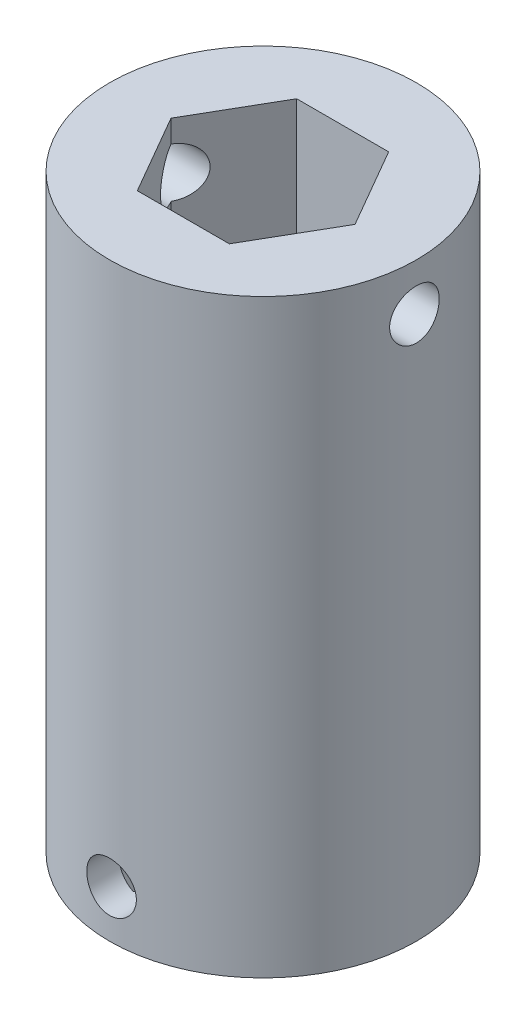
SolidWorks part; units mm, degrees
ref_plane "Front Plane" through (0, 0, 0) normal (0, 0, 1) x (1, 0, 0)
ref_plane "Top Plane" through (0, 0, 0) normal (0, 1, 0) x (1, 0, 0)
ref_plane "Right Plane" through (0, 0, 0) normal (1, 0, 0) x (0, 0, -1)
sketch "Sketch1" plane through (0, 0, 0) normal (0, 1, 0) x (1, 0, 0)
  line L1 (7.7942, 0) -> (3.8971, 6.75)
  line L2 (3.8971, 6.75) -> (-3.8971, 6.75)
  line L3 (-3.8971, 6.75) -> (-7.7942, 0)
  line L4 (-7.7942, 0) -> (-3.8971, -6.75)
  line L5 (-3.8971, -6.75) -> (3.8971, -6.75)
  line L6 (3.8971, -6.75) -> (7.7942, 0)
  circle A0 centre (0, 0) radius 13
  circle A1 centre (0, 0) radius 6.75 construction
  dimension "D2" = 26
  dimension "D1" = 13.5
extrude "Boss-Extrude1" add sketch "Sketch1" along normal blind 30
sketch "Sketch2" plane through (0, 0, 0) normal (0, -1, 0) x (1, 0, 0)
  circle A0 centre (0, 0) radius 13
  dimension "D1" = 26
extrude "Boss-Extrude2" add sketch "Sketch2" along normal blind 20
sketch "Sketch3" plane through (0, -20, 0) normal (0, -1, 0) x (1, 0, 0)
  arc A0 (-6.2438, 8.2671) -> (-5.2142, 5.3944) centre (2.4553, 9.7641) ccw
  arc A1 (-5.2142, 5.3944) -> (-5.5757, 5.0199) centre (0, 0) ccw
  arc A2 (-5.5757, 5.0199) -> (-8.483, 5.9471) centre (-9.671, -2.7995) ccw
  arc A3 (-8.483, 5.9471) -> (-9.2124, 4.7393) centre (0, 0) ccw
  arc A4 (-9.2124, 4.7393) -> (-7.0384, 2.5978) centre (-2.0244, 9.8624) ccw
  arc A5 (-7.0384, 2.5978) -> (-7.2016, 2.1036) centre (0, 0) ccw
  arc A6 (-7.2016, 2.1036) -> (-10.2233, 1.6775) centre (-7.4986, -6.7184) ccw
  arc A7 (-10.2233, 1.6775) -> (-10.3564, 0.2728) centre (0, 0) ccw
  arc A8 (-10.3564, 0.2728) -> (-7.4685, -0.7133) centre (-6.103, 8.0074) ccw
  arc A9 (-7.4685, -0.7133) -> (-7.4011, -1.2294) centre (0, 0) ccw
  arc A10 (-7.4011, -1.2294) -> (-9.9387, -2.9243) centre (-3.841, -9.3066) ccw
  arc A11 (-9.9387, -2.9243) -> (-9.4492, -4.2477) centre (0, 0) ccw
  arc A12 (-9.4492, -4.2477) -> (-6.4194, -3.8831) centre (-8.9729, 4.5664) ccw
  arc A13 (-6.4194, -3.8831) -> (-6.1347, -4.3188) centre (0, 0) ccw
  arc A14 (-6.1347, -4.3188) -> (-7.6857, -6.947) centre (0.5773, -10.0515) ccw
  arc A15 (-7.6857, -6.947) -> (-6.6704, -7.9269) centre (0, 0) ccw
  arc A16 (-6.6704, -7.9269) -> (-4.0989, -6.2838) centre (-10.0656, 0.221) ccw
  arc A17 (-4.0989, -6.2838) -> (-3.6533, -6.5529) centre (0, 0) ccw
  arc A18 (-3.6533, -6.5529) -> (-3.9104, -9.5937) centre (4.8813, -8.8056) ccw
  arc A19 (-3.9104, -9.5937) -> (-2.5705, -10.036) centre (0, 0) ccw
  arc A20 (-2.5705, -10.036) -> (-0.9665, -7.44) centre (-9.1647, -4.1682) ccw
  arc A21 (-0.9665, -7.44) -> (-0.4483, -7.4891) centre (0, 0) ccw
  arc A22 (-0.4483, -7.4891) -> (0.6394, -10.3402) centre (8.2185, -5.8156) ccw
  arc A23 (0.6394, -10.3402) -> (2.0385, -10.1575) centre (0, 0) ccw
  arc A24 (2.0385, -10.1575) -> (2.3573, -7.1225) centre (-6.4486, -7.7318) ccw
  arc A25 (2.3573, -7.1225) -> (2.8455, -6.942) centre (0, 0) ccw
  arc A26 (2.8455, -6.942) -> (5.0626, -9.0388) centre (9.9279, -1.6738) ccw
  arc A27 (5.0626, -9.0388) -> (6.2438, -8.2671) centre (0, 0) ccw
  arc A28 (6.2438, -8.2671) -> (5.2142, -5.3944) centre (-2.4553, -9.7641) ccw
  arc A29 (5.2142, -5.3944) -> (5.5757, -5.0199) centre (0, 0) ccw
  arc A30 (5.5757, -5.0199) -> (8.483, -5.9471) centre (9.671, 2.7995) ccw
  arc A31 (8.483, -5.9471) -> (9.2124, -4.7393) centre (0, 0) ccw
  arc A32 (9.2124, -4.7393) -> (7.0384, -2.5978) centre (2.0244, -9.8624) ccw
  arc A33 (7.0384, -2.5978) -> (7.2016, -2.1036) centre (0, 0) ccw
  arc A34 (7.2016, -2.1036) -> (10.2233, -1.6775) centre (7.4986, 6.7184) ccw
  arc A35 (10.2233, -1.6775) -> (10.3564, -0.2728) centre (0, 0) ccw
  arc A36 (10.3564, -0.2728) -> (7.4685, 0.7133) centre (6.103, -8.0074) ccw
  arc A37 (7.4685, 0.7133) -> (7.4011, 1.2294) centre (0, 0) ccw
  arc A38 (7.4011, 1.2294) -> (9.9387, 2.9243) centre (3.841, 9.3066) ccw
  arc A39 (9.9387, 2.9243) -> (9.4492, 4.2477) centre (0, 0) ccw
  arc A40 (9.4492, 4.2477) -> (6.4194, 3.8831) centre (8.9729, -4.5664) ccw
  arc A41 (6.4194, 3.8831) -> (6.1347, 4.3188) centre (0, 0) ccw
  arc A42 (6.1347, 4.3188) -> (7.6857, 6.947) centre (-0.5773, 10.0515) ccw
  arc A43 (7.6857, 6.947) -> (6.6704, 7.9269) centre (0, 0) ccw
  arc A44 (6.6704, 7.9269) -> (4.0989, 6.2838) centre (10.0656, -0.221) ccw
  arc A45 (4.0989, 6.2838) -> (3.6533, 6.5529) centre (0, 0) ccw
  arc A46 (3.6533, 6.5529) -> (3.9104, 9.5937) centre (-4.8813, 8.8056) ccw
  arc A47 (3.9104, 9.5937) -> (2.5705, 10.036) centre (0, 0) ccw
  arc A48 (2.5705, 10.036) -> (0.9665, 7.44) centre (9.1647, 4.1682) ccw
  arc A49 (0.9665, 7.44) -> (0.4483, 7.4891) centre (0, 0) ccw
  arc A50 (0.4483, 7.4891) -> (-0.6394, 10.3402) centre (-8.2185, 5.8156) ccw
  arc A51 (-0.6394, 10.3402) -> (-2.0385, 10.1575) centre (0, 0) ccw
  arc A52 (-2.0385, 10.1575) -> (-2.3573, 7.1225) centre (6.4486, 7.7318) ccw
  arc A53 (-2.3573, 7.1225) -> (-2.8455, 6.942) centre (0, 0) ccw
  arc A54 (-2.8455, 6.942) -> (-5.0626, 9.0388) centre (-9.9279, 1.6738) ccw
  arc A55 (-5.0626, 9.0388) -> (-6.2438, 8.2671) centre (0, 0) ccw
  arc A57 (-5.5304, 4.7688) -> (-8.3889, 5.7316) centre (-9.671, -2.7995) ccw
  arc A58 (-4.9617, 5.358) -> (-5.5304, 4.7688) centre (0, 0) ccw
  arc A59 (-6.0251, 8.1807) -> (-4.9617, 5.358) centre (2.4553, 9.7641) ccw
  arc A60 (-5.0713, 8.8038) -> (-6.0251, 8.1807) centre (0, 0) ccw
  arc A61 (-2.9136, 6.6961) -> (-5.0713, 8.8038) centre (-9.9279, 1.6738) ccw
  arc A62 (-2.1455, 6.9802) -> (-2.9136, 6.6961) centre (0, 0) ccw
  arc A63 (-1.879, 9.9847) -> (-2.1455, 6.9802) centre (6.4486, 7.7318) ccw
  arc A64 (-0.7492, 10.1323) -> (-1.879, 9.9847) centre (0, 0) ccw
  arc A65 (0.2803, 7.2971) -> (-0.7492, 10.1323) centre (-8.2185, 5.8156) ccw
  arc A66 (1.0955, 7.2199) -> (0.2803, 7.2971) centre (0, 0) ccw
  arc A67 (2.6393, 9.8112) -> (1.0955, 7.2199) centre (9.1647, 4.1682) ccw
  arc A68 (3.7212, 9.454) -> (2.6393, 9.8112) centre (0, 0) ccw
  arc A69 (3.4186, 6.4529) -> (3.7212, 9.454) centre (-4.8813, 8.8056) ccw
  arc A70 (4.1196, 6.0295) -> (3.4186, 6.4529) centre (0, 0) ccw
  arc A71 (6.6349, 7.6944) -> (4.1196, 6.0295) centre (10.0656, -0.221) ccw
  arc A72 (7.4546, 6.9032) -> (6.6349, 7.6944) centre (0, 0) ccw
  arc A73 (5.8799, 4.3306) -> (7.4546, 6.9032) centre (-0.5773, 10.0515) ccw
  arc A74 (6.3278, 3.645) -> (5.8799, 4.3306) centre (0, 0) ccw
  arc A75 (9.3163, 4.0537) -> (6.3278, 3.645) centre (8.9729, -4.5664) ccw
  arc A76 (9.7116, 2.9851) -> (9.3163, 4.0537) centre (0, 0) ccw
  arc A77 (7.1765, 1.3505) -> (9.7116, 2.9851) centre (3.841, 9.3066) ccw
  arc A78 (7.2826, 0.5385) -> (7.1765, 1.3505) centre (0, 0) ccw
  arc A79 (10.1525, -0.3899) -> (7.2826, 0.5385) centre (6.103, -8.0074) ccw
  arc A80 (10.045, -1.5242) -> (10.1525, -0.3899) centre (0, 0) ccw
  arc A81 (7.0518, -1.897) -> (10.045, -1.5242) centre (7.4986, 6.7184) ccw
  arc A82 (6.7951, -2.6746) -> (7.0518, -1.897) centre (0, 0) ccw
  arc A83 (8.9779, -4.7563) -> (6.7951, -2.6746) centre (2.0244, -9.8624) ccw
  arc A84 (8.3889, -5.7316) -> (8.9779, -4.7563) centre (0, 0) ccw
  arc A85 (5.5304, -4.7688) -> (8.3889, -5.7316) centre (9.671, 2.7995) ccw
  arc A86 (4.9617, -5.358) -> (5.5304, -4.7688) centre (0, 0) ccw
  arc A87 (6.0251, -8.1807) -> (4.9617, -5.358) centre (-2.4553, -9.7641) ccw
  arc A88 (5.0713, -8.8038) -> (6.0251, -8.1807) centre (0, 0) ccw
  arc A89 (2.9136, -6.6961) -> (5.0713, -8.8038) centre (9.9279, -1.6738) ccw
  arc A90 (2.1455, -6.9802) -> (2.9136, -6.6961) centre (0, 0) ccw
  arc A91 (1.879, -9.9847) -> (2.1455, -6.9802) centre (-6.4486, -7.7318) ccw
  arc A92 (0.7492, -10.1323) -> (1.879, -9.9847) centre (0, 0) ccw
  arc A93 (-0.2803, -7.2971) -> (0.7492, -10.1323) centre (8.2185, -5.8156) ccw
  arc A94 (-1.0955, -7.2199) -> (-0.2803, -7.2971) centre (0, 0) ccw
  arc A95 (-2.6393, -9.8112) -> (-1.0955, -7.2199) centre (-9.1647, -4.1682) ccw
  arc A96 (-3.7212, -9.454) -> (-2.6393, -9.8112) centre (0, 0) ccw
  arc A97 (-3.4186, -6.4529) -> (-3.7212, -9.454) centre (4.8813, -8.8056) ccw
  arc A98 (-4.1196, -6.0295) -> (-3.4186, -6.4529) centre (0, 0) ccw
  arc A99 (-6.6349, -7.6944) -> (-4.1196, -6.0295) centre (-10.0656, 0.221) ccw
  arc A100 (-7.4546, -6.9032) -> (-6.6349, -7.6944) centre (0, 0) ccw
  arc A101 (-5.8799, -4.3306) -> (-7.4546, -6.9032) centre (0.5773, -10.0515) ccw
  arc A102 (-6.3278, -3.645) -> (-5.8799, -4.3306) centre (0, 0) ccw
  arc A103 (-9.3163, -4.0537) -> (-6.3278, -3.645) centre (-8.9729, 4.5664) ccw
  arc A104 (-9.7116, -2.9851) -> (-9.3163, -4.0537) centre (0, 0) ccw
  arc A105 (-7.1765, -1.3505) -> (-9.7116, -2.9851) centre (-3.841, -9.3066) ccw
  arc A106 (-7.2826, -0.5385) -> (-7.1765, -1.3505) centre (0, 0) ccw
  arc A107 (-10.1525, 0.3899) -> (-7.2826, -0.5385) centre (-6.103, 8.0074) ccw
  arc A108 (-10.045, 1.5242) -> (-10.1525, 0.3899) centre (0, 0) ccw
  arc A109 (-7.0518, 1.897) -> (-10.045, 1.5242) centre (-7.4986, -6.7184) ccw
  arc A110 (-6.7951, 2.6746) -> (-7.0518, 1.897) centre (0, 0) ccw
  arc A111 (-8.9779, 4.7563) -> (-6.7951, 2.6746) centre (-2.0244, 9.8624) ccw
  arc A112 (-8.3889, 5.7316) -> (-8.9779, 4.7563) centre (0, 0) ccw
  arc A113 (-5.5304, 4.7688) -> (-8.3889, 5.7316) centre (-9.671, -2.7995) ccw construction
  arc A114 (-4.9617, 5.358) -> (-5.5304, 4.7688) centre (0, 0) ccw construction
  arc A115 (-6.0251, 8.1807) -> (-4.9617, 5.358) centre (2.4553, 9.7641) ccw construction
  arc A116 (-5.0713, 8.8038) -> (-6.0251, 8.1807) centre (0, 0) ccw construction
  arc A117 (-2.9136, 6.6961) -> (-5.0713, 8.8038) centre (-9.9279, 1.6738) ccw construction
  arc A118 (-2.1455, 6.9802) -> (-2.9136, 6.6961) centre (0, 0) ccw construction
  arc A119 (-1.879, 9.9847) -> (-2.1455, 6.9802) centre (6.4486, 7.7318) ccw construction
  arc A120 (-0.7492, 10.1323) -> (-1.879, 9.9847) centre (0, 0) ccw construction
  arc A121 (0.2803, 7.2971) -> (-0.7492, 10.1323) centre (-8.2185, 5.8156) ccw construction
  arc A122 (1.0955, 7.2199) -> (0.2803, 7.2971) centre (0, 0) ccw construction
  arc A123 (2.6393, 9.8112) -> (1.0955, 7.2199) centre (9.1647, 4.1682) ccw construction
  arc A124 (3.7212, 9.454) -> (2.6393, 9.8112) centre (0, 0) ccw construction
  arc A125 (3.4186, 6.4529) -> (3.7212, 9.454) centre (-4.8813, 8.8056) ccw construction
  arc A126 (4.1196, 6.0295) -> (3.4186, 6.4529) centre (0, 0) ccw construction
  arc A127 (6.6349, 7.6944) -> (4.1196, 6.0295) centre (10.0656, -0.221) ccw construction
  arc A128 (7.4546, 6.9032) -> (6.6349, 7.6944) centre (0, 0) ccw construction
  arc A129 (5.8799, 4.3306) -> (7.4546, 6.9032) centre (-0.5773, 10.0515) ccw construction
  arc A130 (6.3278, 3.645) -> (5.8799, 4.3306) centre (0, 0) ccw construction
  arc A131 (9.3163, 4.0537) -> (6.3278, 3.645) centre (8.9729, -4.5664) ccw construction
  arc A132 (9.7116, 2.9851) -> (9.3163, 4.0537) centre (0, 0) ccw construction
  arc A133 (7.1765, 1.3505) -> (9.7116, 2.9851) centre (3.841, 9.3066) ccw construction
  arc A134 (7.2826, 0.5385) -> (7.1765, 1.3505) centre (0, 0) ccw construction
  arc A135 (10.1525, -0.3899) -> (7.2826, 0.5385) centre (6.103, -8.0074) ccw construction
  arc A136 (10.045, -1.5242) -> (10.1525, -0.3899) centre (0, 0) ccw construction
  arc A137 (7.0518, -1.897) -> (10.045, -1.5242) centre (7.4986, 6.7184) ccw construction
  arc A138 (6.7951, -2.6746) -> (7.0518, -1.897) centre (0, 0) ccw construction
  arc A139 (8.9779, -4.7563) -> (6.7951, -2.6746) centre (2.0244, -9.8624) ccw construction
  arc A140 (8.3889, -5.7316) -> (8.9779, -4.7563) centre (0, 0) ccw construction
  arc A141 (5.5304, -4.7688) -> (8.3889, -5.7316) centre (9.671, 2.7995) ccw construction
  arc A142 (4.9617, -5.358) -> (5.5304, -4.7688) centre (0, 0) ccw construction
  arc A143 (6.0251, -8.1807) -> (4.9617, -5.358) centre (-2.4553, -9.7641) ccw construction
  arc A144 (5.0713, -8.8038) -> (6.0251, -8.1807) centre (0, 0) ccw construction
  arc A145 (2.9136, -6.6961) -> (5.0713, -8.8038) centre (9.9279, -1.6738) ccw construction
  arc A146 (2.1455, -6.9802) -> (2.9136, -6.6961) centre (0, 0) ccw construction
  arc A147 (1.879, -9.9847) -> (2.1455, -6.9802) centre (-6.4486, -7.7318) ccw construction
  arc A148 (0.7492, -10.1323) -> (1.879, -9.9847) centre (0, 0) ccw construction
  arc A149 (-0.2803, -7.2971) -> (0.7492, -10.1323) centre (8.2185, -5.8156) ccw construction
  arc A150 (-1.0955, -7.2199) -> (-0.2803, -7.2971) centre (0, 0) ccw construction
  arc A151 (-2.6393, -9.8112) -> (-1.0955, -7.2199) centre (-9.1647, -4.1682) ccw construction
  arc A152 (-3.7212, -9.454) -> (-2.6393, -9.8112) centre (0, 0) ccw construction
  arc A153 (-3.4186, -6.4529) -> (-3.7212, -9.454) centre (4.8813, -8.8056) ccw construction
  arc A154 (-4.1196, -6.0295) -> (-3.4186, -6.4529) centre (0, 0) ccw construction
  arc A155 (-6.6349, -7.6944) -> (-4.1196, -6.0295) centre (-10.0656, 0.221) ccw construction
  arc A156 (-7.4546, -6.9032) -> (-6.6349, -7.6944) centre (0, 0) ccw construction
  arc A157 (-5.8799, -4.3306) -> (-7.4546, -6.9032) centre (0.5773, -10.0515) ccw construction
  arc A158 (-6.3278, -3.645) -> (-5.8799, -4.3306) centre (0, 0) ccw construction
  arc A159 (-9.3163, -4.0537) -> (-6.3278, -3.645) centre (-8.9729, 4.5664) ccw construction
  arc A160 (-9.7116, -2.9851) -> (-9.3163, -4.0537) centre (0, 0) ccw construction
  arc A161 (-7.1765, -1.3505) -> (-9.7116, -2.9851) centre (-3.841, -9.3066) ccw construction
  arc A162 (-7.2826, -0.5385) -> (-7.1765, -1.3505) centre (0, 0) ccw construction
  arc A163 (-10.1525, 0.3899) -> (-7.2826, -0.5385) centre (-6.103, 8.0074) ccw construction
  arc A164 (-10.045, 1.5242) -> (-10.1525, 0.3899) centre (0, 0) ccw construction
  arc A165 (-7.0518, 1.897) -> (-10.045, 1.5242) centre (-7.4986, -6.7184) ccw construction
  arc A166 (-6.7951, 2.6746) -> (-7.0518, 1.897) centre (0, 0) ccw construction
  arc A167 (-8.9779, 4.7563) -> (-6.7951, 2.6746) centre (-2.0244, 9.8624) ccw construction
  arc A168 (-8.3889, 5.7316) -> (-8.9779, 4.7563) centre (0, 0) ccw construction
  dimension "D1" = 0
  dimension "D2" = 0.2
extrude "Cut-Extrude1" cut sketch "Sketch3" against normal blind 23
sketch "Sketch4" plane through (0, 0, 0) normal (0, 0, 1) x (1, 0, 0)
  line L0 (-13, -20) -> (13, -20) construction
  circle A0 centre (0, -16) radius 2.1
  point P2 (0, 0)
  dimension "D1" = 4.2
  dimension "D2" = 4
extrude "Cut-Extrude2" cut sketch "Sketch4" against normal through all and the other way through all
sketch "Sketch5" plane through (0, 0, 0) normal (1, 0, 0) x (0, 0, -1)
  line L0 (13, 30) -> (-13, 30) construction
  circle A0 centre (0, 26) radius 2.1
  dimension "D2" = 4.2
  dimension "D1" = 4
extrude "Cut-Extrude3" cut sketch "Sketch5" against normal through all and the other way through all
